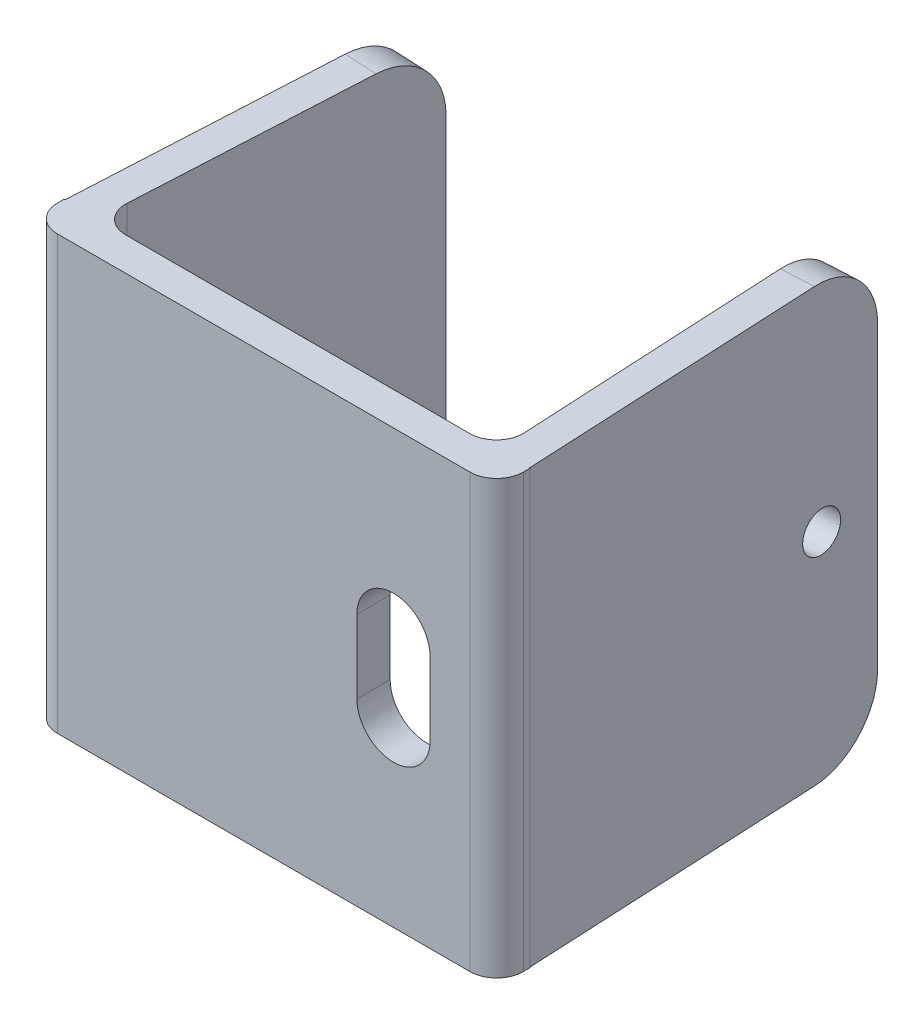
SolidWorks part; units mm, degrees
ref_plane "前视基准面" through (0, 0, 0) normal (0, 0, 1) x (1, 0, 0)
ref_plane "上视基准面" through (0, 0, 0) normal (0, 1, 0) x (1, 0, 0)
ref_plane "右视基准面" through (0, 0, 0) normal (1, 0, 0) x (0, 0, -1)
other "Configuration Table"
sketch "草图1" plane through (0, 0, 0) normal (0, 0, 1) x (1, 0, 0)
  line L1 (17.5, -16.25) -> (-17.5, -16.25)
  line L2 (17.5, -16.25) -> (17.5, 16.25)
  line L3 (17.5, 16.25) -> (-17.5, 16.25)
  line L4 (-17.5, -16.25) -> (-17.5, 16.25)
  line L5 (17.5, -16.25) -> (-17.5, 16.25) construction
  line L6 (17.5, 16.25) -> (-17.5, -16.25) construction
  point P0 (0, 0)
  dimension "D1" = 32.5
  dimension "D2" = 35
extrude "凸台-拉伸1" add sketch "草图1" along normal blind 2.5
sketch "草图2" plane through (0, -16.25, 0) normal (0, -1, 0) x (1, 0, 0)
  line L0 (-13.6759, -24.8719) -> (-14.9828, 0.0549)
  line L2 (-17.5, 2.5) -> (17.5, 2.5) construction
  line L3 (-14.9828, 0.0549) -> (-17.4322, 0.0549)
  line L4 (-17.4322, 0.0549) -> (-16.1186, -25)
  line L5 (-16.1186, -25) -> (-13.6759, -24.8719)
  line L6 (17.5, 2.5) -> (17.5, 0) construction
  line L8 (16.1186, -27.5) -> (13.6759, -27.3719)
  line L9 (17.5, 0.8231) -> (16.1186, -27.5)
  line L10 (15.1086, 0.3058) -> (17.5, 0.8231)
  line L11 (13.6759, -27.3719) -> (15.1086, 0.3058)
  point P4 (17.5834, 0.4885)
  point P5 (17.5, 0.4873)
  point P10 (15.1086, 0.3058)
  dimension "D1" = 27.5
  dimension "D2" = 30
  dimension "D3" = 2.4468
extrude "凸台-拉伸2" add sketch "草图2" against normal up to surface (32.5 mm away) up to face at (0, 16.25, 1.25)
fillet "圆角1" radius 2 4 edges at (15.0927, 0, 0) (-14.9799, 0, 0) (-17.5, 0, 2.5) (17.5, 0, 2.5)
fillet "圆角2" radius 5 4 edges at (14.8973, 16.25, -27.436) (14.8973, -16.25, -27.436) (-14.8973, 16.25, -24.936) (-14.8973, -16.25, -24.936)
sketch "草图3" plane through (17.4184, 0, -0.8496) normal (0.9988, 0, -0.0487) x (-0.0487, 0, -0.9988)
  line L0 (26.6821, 0) -> (18.6254, 0) construction
  line L1 (26.6821, 11.25) -> (26.6821, -11.25) construction
  circle A0 centre (22.2566, 0) radius 1.5
  dimension "D1" = 3
extrude "切除-拉伸1" cut sketch "草图3" against normal blind 10
sketch "草图4" plane through (0, 0, 2.5) normal (0, 0, 1) x (1, 0, 0)
  line L0 (9.75, 2.75) -> (9.75, -2.75) construction
  line L1 (12.5, 2.75) -> (12.5, -2.75)
  line L2 (7, 2.75) -> (7, -2.75)
  line L3 (15.5, -16.25) -> (15.5, 16.25) construction
  arc A0 (12.5, 2.75) -> (7, 2.75) centre (9.75, 2.75) ccw
  arc A1 (7, -2.75) -> (12.5, -2.75) centre (9.75, -2.75) ccw
  point P2 (9.75, 0)
  point P7 (9.75, 5.5)
  point P8 (9.75, -5.5)
  dimension "D1" = 11
  dimension "D2" = 0
  dimension "D3" = 5.5
  dimension "D4" = 3
extrude "切除-拉伸2" cut sketch "草图4" against normal blind 10
